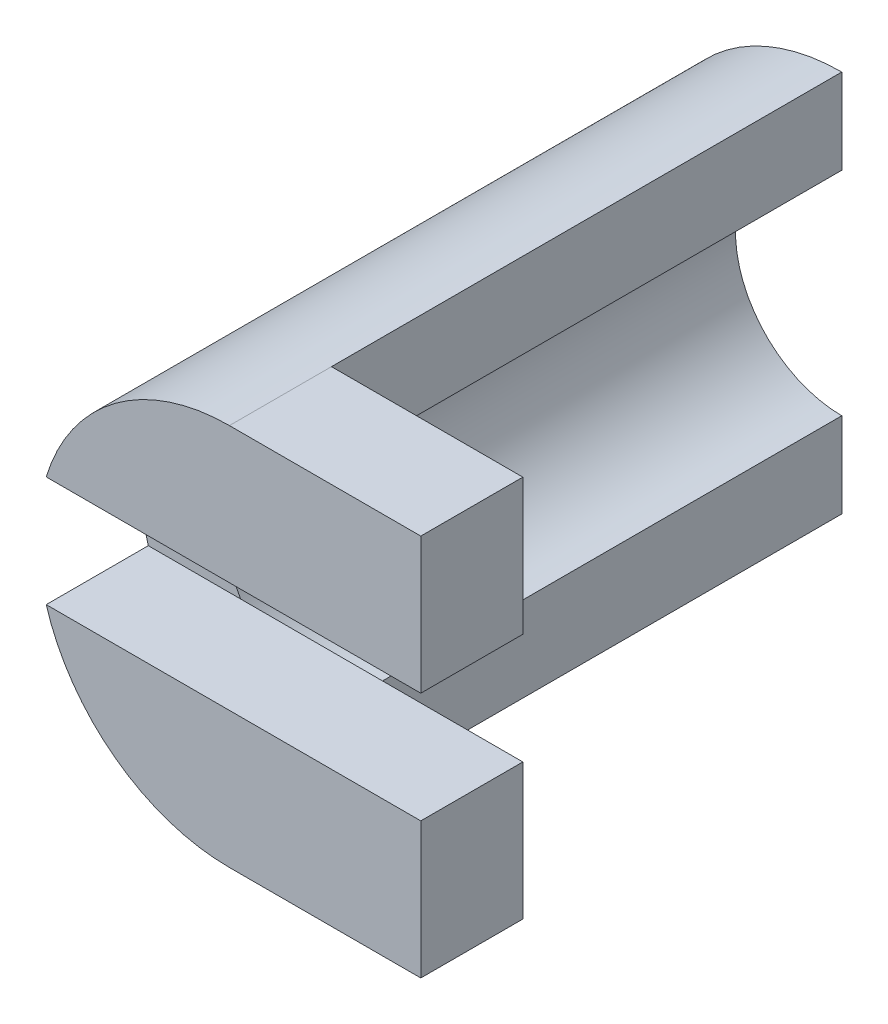
SolidWorks part; units mm, degrees
ref_plane "前视基准面" through (0, 0, 0) normal (0, 0, 1) x (1, 0, 0)
ref_plane "上视基准面" through (0, 0, 0) normal (0, 1, 0) x (1, 0, 0)
ref_plane "右视基准面" through (0, 0, 0) normal (1, 0, 0) x (0, 0, -1)
other "Configuration Table"
sketch "草图1" plane through (0, 0, 0) normal (0, 0, 1) x (1, 0, 0)
  line L0 (0, 0) -> (0, 20047.4616) construction
  line L1 (0, 6.25) -> (0, 11.25)
  line L2 (0, -6.25) -> (0, -11.25)
  arc A0 (0, 11.25) -> (0, -11.25) centre (0, 0) ccw
  arc A1 (0, 6.25) -> (0, -6.25) centre (0, 0) ccw
  dimension "D1" = 5
  dimension "D2" = 6.25
extrude "凸台-拉伸1" add sketch "草图1" along normal blind 30
sketch "草图2" plane through (0, 0, 30) normal (0, 0, 1) x (1, 0, 0)
  line L1 (11.25, 11.25) -> (-11.25, 11.25)
  line L2 (11.25, 11.25) -> (11.25, -11.25)
  line L3 (11.25, -11.25) -> (-11.25, -11.25)
  line L4 (-11.25, 11.25) -> (-11.25, -11.25)
  line L5 (11.25, 11.25) -> (-11.25, -11.25) construction
  line L6 (11.25, -11.25) -> (-11.25, 11.25) construction
  line L7 (-11.25, 3.25) -> (11.25, 3.25)
  line L8 (-11.25, 3.25) -> (-11.25, -3.25)
  line L9 (-11.25, -3.25) -> (11.25, -3.25)
  line L10 (11.25, 3.25) -> (11.25, -3.25)
  line L11 (-11.25, 3.25) -> (11.25, -3.25) construction
  line L12 (-11.25, -3.25) -> (11.25, 3.25) construction
  arc A0 (0, 11.25) -> (0, -11.25) centre (0, 0) ccw construction
  point P0 (0, 0)
  point P9 (0, 0)
  arc M3 (0, -6.25) -> (0, 6.25) centre (0, 0) cw
  line M4 (0, 6.25) -> (0, 11.25)
  arc M5 (0, 11.25) -> (0, -11.25) centre (0, 0) ccw
  line M6 (0, -11.25) -> (0, -6.25)
  dimension "D1" = 6.5
extrude "凸台-拉伸2" add sketch "草图2" along normal blind 6 contours L7 M5 M3 M4 | L7 L2 L1 M3 M4 | L9 M5 M6 M3 | L9 L3 L2 M3 M6
ref_plane "基准面1" through (-6.25, 0, 0) normal (1, 0, 0) x (0, 0, -1)
sketch "草图3" plane through (-6.25, 0, 0) normal (1, 0, 0) x (0, 0, -1)
  line L0 (-30, 11.25) -> (0, 11.25) construction
  line L1 (-30, 11.25) -> (0, 11.25)
  line L2 (-1000, 0) -> (49000, 0) construction
  line L3 (0, -11.25) -> (0, 11.25) construction
  line L4 (-30, 6.25) -> (0, 6.25) construction
  line L5 (-30, 6.25) -> (0, 6.25)
  circle A0 centre (-24.662, 11.25) radius 2.1476
  point P7 (0, 0)
